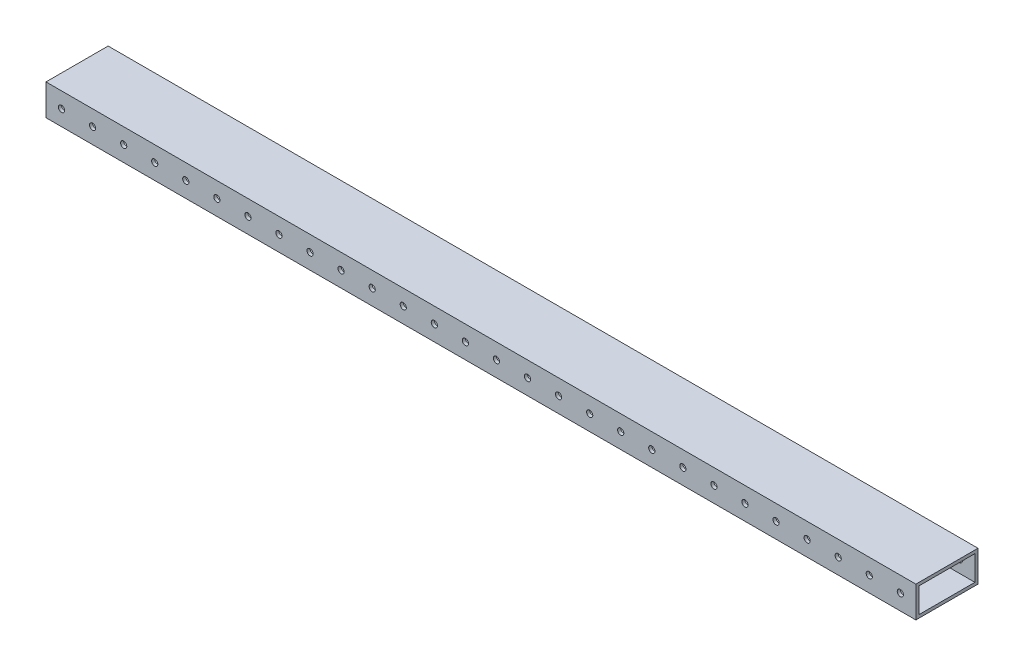
SolidWorks part; units mm, degrees
ref_plane "Front Plane" through (0, 0, 0) normal (0, 0, 1) x (1, 0, 0)
ref_plane "Top Plane" through (0, 0, 0) normal (0, 1, 0) x (1, 0, 0)
ref_plane "Right Plane" through (0, 0, 0) normal (1, 0, 0) x (0, 0, -1)
sketch "Sketch2" plane through (0, 0, 0) normal (1, 0, 0) x (0, 0, -1)
  line L0 (2.54, 2.54) -> (2.54, 22.86)
  line L1 (0, 0) -> (50.8, 0)
  line L2 (0, 0) -> (0, 25.4)
  line L3 (0, 25.4) -> (50.8, 25.4)
  line L4 (50.8, 0) -> (50.8, 25.4)
  line L5 (2.54, 22.86) -> (48.26, 22.86)
  line L6 (48.26, 2.54) -> (48.26, 22.86)
  line L7 (2.54, 2.54) -> (48.26, 2.54)
  dimension "D1" = 50.8
  dimension "D2" = 25.4
  dimension "D3" = 2.54
extrude "Boss-Extrude1" add sketch "Sketch2" along normal blind 711.2
sketch "Sketch3" plane through (0, 0, 0) normal (0, 0, 1) x (1, 0, 0)
  line L0 (0, 25.4) -> (0, 0) construction
  line L1 (711.2, 25.4) -> (0, 25.4) construction
  circle A0 centre (12.7, 12.7) radius 2.54
  dimension "D1" = 5.08
  dimension "D2" = 12.7
  dimension "D3" = 12.7
extrude "Cut-Extrude1" cut sketch "Sketch3" against normal through all
pattern_linear "LPattern1" count 28 spacing 25.4 along (1, 0, 0) of "Cut-Extrude1"
